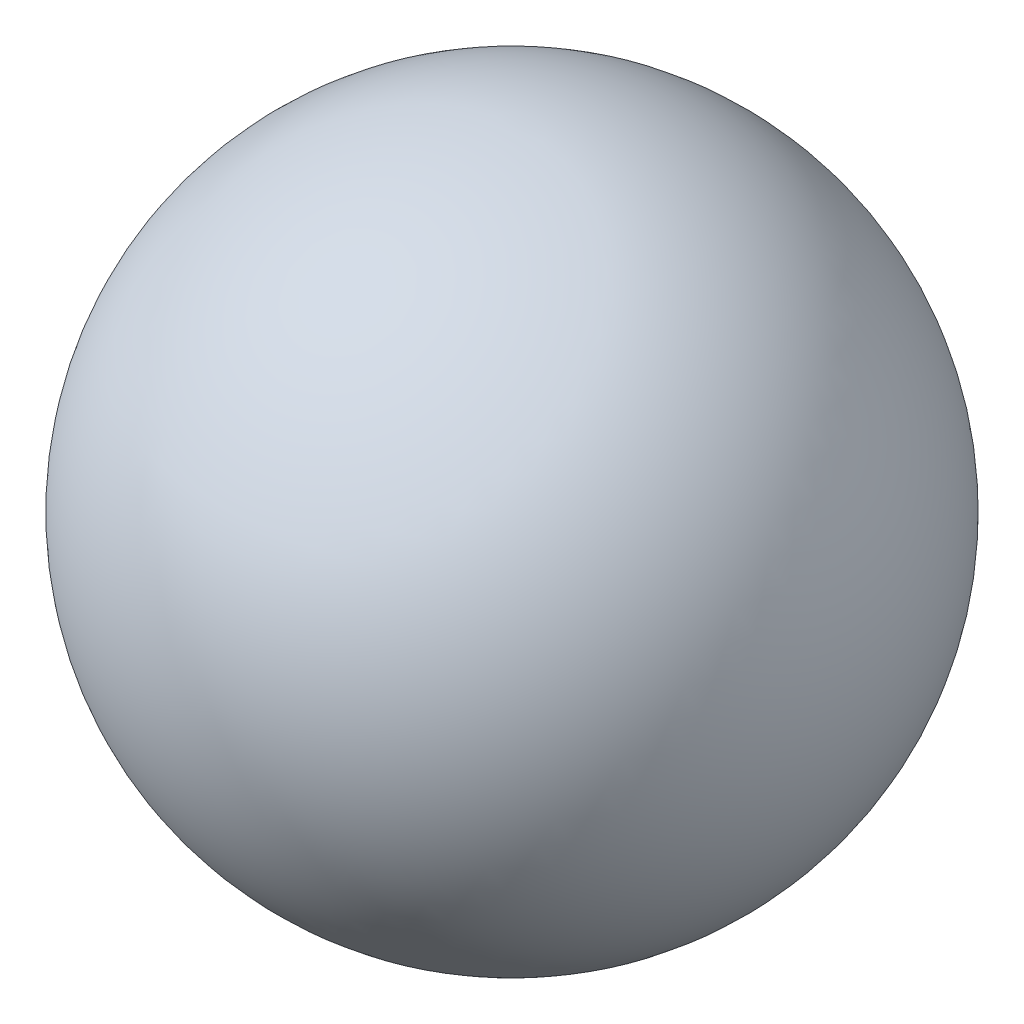
SolidWorks part; units mm, degrees
ref_plane "Front Plane" through (0, 0, 0) normal (0, 0, 1) x (1, 0, 0)
ref_plane "Top Plane" through (0, 0, 0) normal (0, 1, 0) x (1, 0, 0)
ref_plane "Right Plane" through (0, 0, 0) normal (1, 0, 0) x (0, 0, -1)
sketch "Sketch1" plane through (0, 0, 0) normal (0, 0, 1) x (1, 0, 0)
  line L0 (0, -65) -> (0, 65)
  arc A0 (0, 65) -> (0, -65) centre (0, 0) ccw
  point P5 (0, 0)
  dimension "D1" = 130
revolve "Revolve1" add sketch "Sketch1" angle 360 about L0
